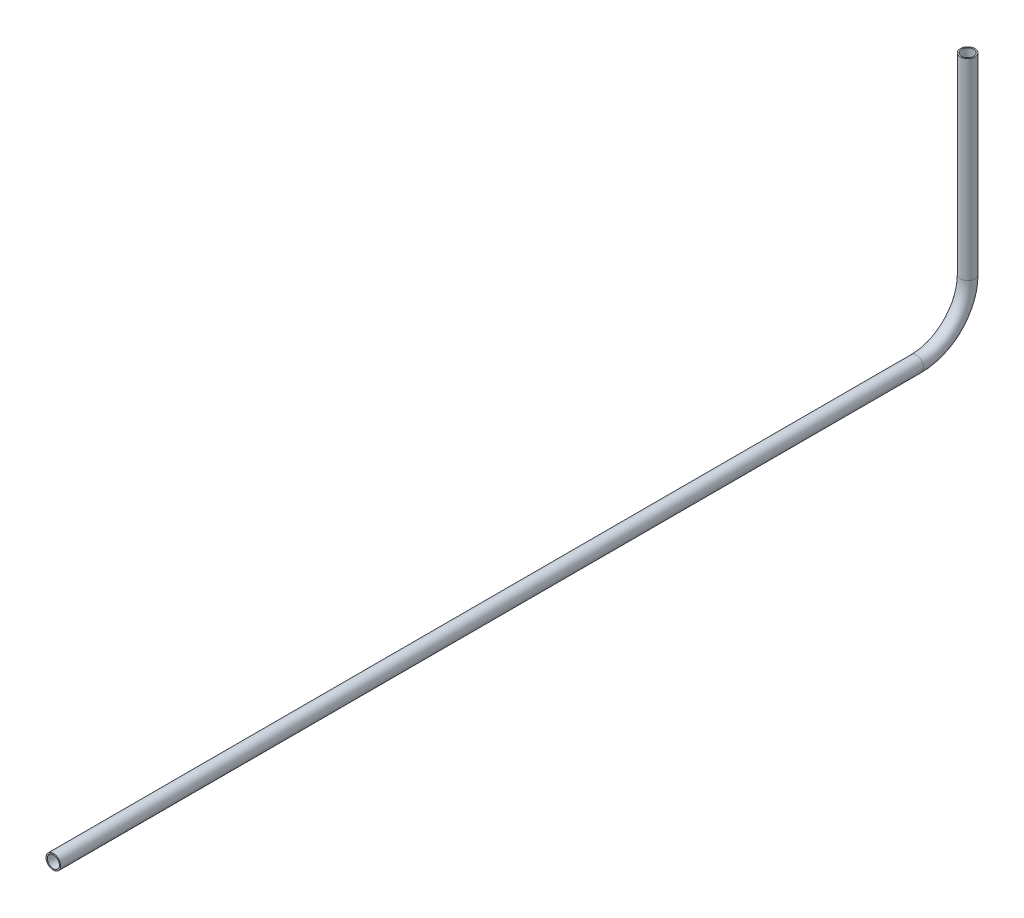
SolidWorks part; units mm, degrees
ref_plane "Front Plane" through (0, 0, 0) normal (0, 0, 1) x (1, 0, 0)
ref_plane "Top Plane" through (0, 0, 0) normal (0, 1, 0) x (1, 0, 0)
ref_plane "Right Plane" through (0, 0, 0) normal (1, 0, 0) x (0, 0, -1)
sketch "Sketch1" plane through (0, 0, 0) normal (1, 0, 0) x (0, 0, -1)
  line L0 (-242.9176, 192.007) -> (131.1171, 192.007)
  line L1 (153.3421, 214.232) -> (153.3421, 297.5279)
  arc A0 (131.1171, 192.007) -> (153.3421, 214.232) centre (131.1171, 214.232) ccw
  point P2 (84.9839, 297.4335)
  point P6 (153.5863, 298.6779)
  point P7 (0, 0)
  point P8 (153.3144, 297.504)
  point P10 (153.3421, 297.5279)
  dimension "D1" = 22.225
other "Pipe 0.5 SCH 40(1)"
ref_plane "Plane1" through (0, 192.007, 242.9176) normal (0, 0, -1) x (0, 1, 0)
sketch "Sketch11" plane through (0, 192.007, 242.9176) normal (0, 0, -1) x (0, 1, 0)
  circle A0 centre (0, 0) radius 3.175
  circle A1 centre (0, 0) radius 2.6162
  point P5 (0, 0)
  dimension "In_dia" = 6.35
  dimension "Out_dia" = 5.2324
